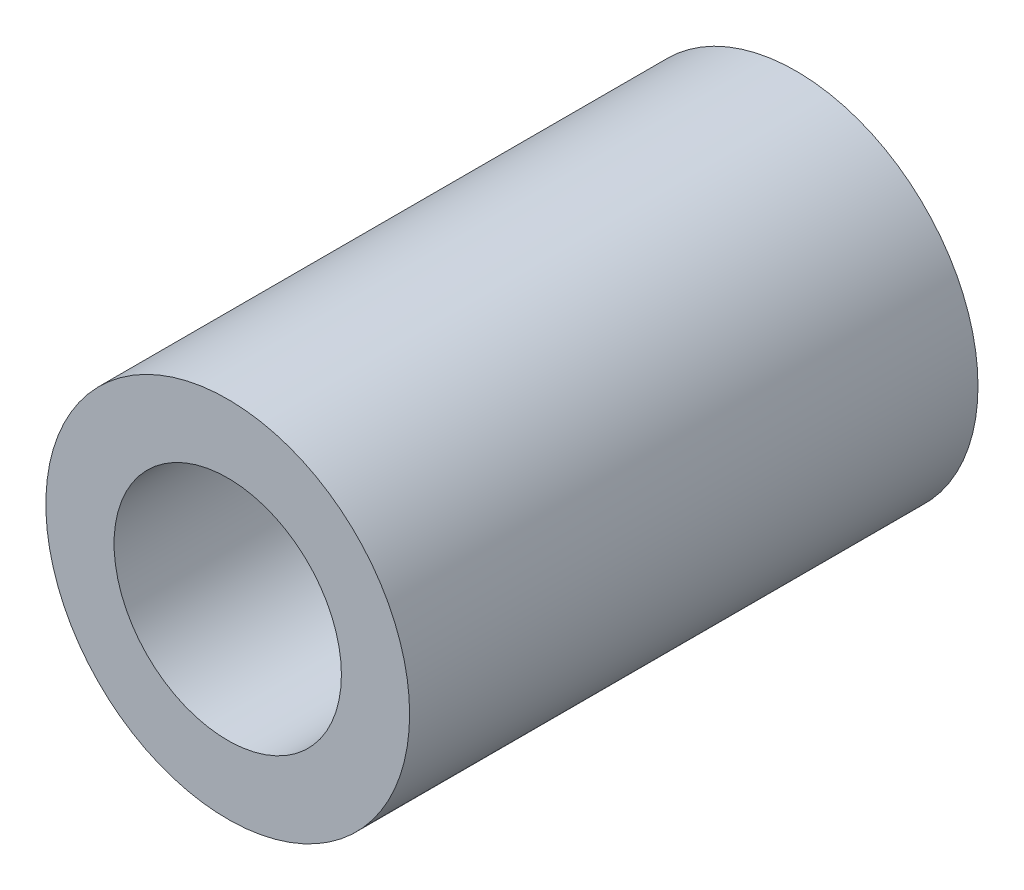
SolidWorks part; units mm, degrees
material "6061-T6 (SS)"
ref_plane "Front Plane" through (0, 0, 0) normal (0, 0, 1) x (1, 0, 0)
ref_plane "Top Plane" through (0, 0, 0) normal (0, 1, 0) x (1, 0, 0)
ref_plane "Right Plane" through (0, 0, 0) normal (1, 0, 0) x (0, 0, -1)
sketch "Sketch1" plane through (0, 0, 0) normal (0, 0, 1) x (1, 0, 0)
  circle A0 centre (84.25, 0) radius 8
  circle A1 centre (84.25, 0) radius 5
  dimension "D1" = 10
  dimension "D2" = 16
extrude "Boss-Extrude1" add sketch "Sketch1" along normal blind 25
